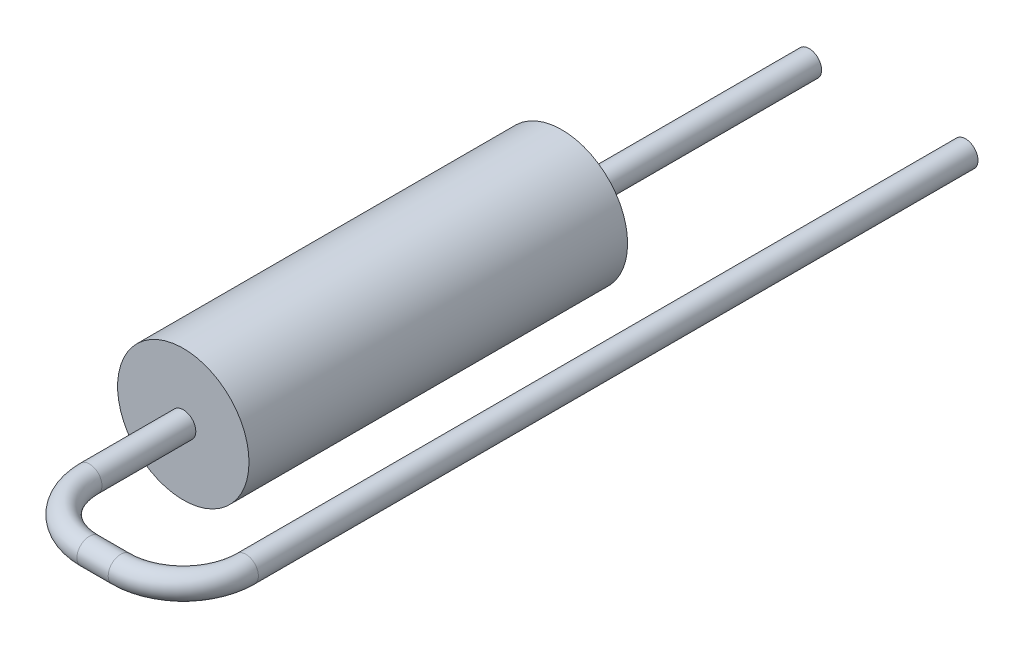
SolidWorks part; units mm, degrees
ref_plane "Front Plane" through (0, 0, 0) normal (0, 0, 1) x (1, 0, 0)
ref_plane "Top Plane" through (0, 0, 0) normal (0, 1, 0) x (1, 0, 0)
ref_plane "Right Plane" through (0, 0, 0) normal (1, 0, 0) x (0, 0, -1)
sketch "Sketch2" plane through (0, 0, 0) normal (0, 0, 1) x (1, 0, 0)
  circle A0 centre (0, 0) radius 2.1
  dimension "D1" = 4.2
extrude "Resistor Body" add sketch "Sketch2" along normal blind 12.1
sketch "Lead1 Path" plane through (0, 0, 0) normal (0, 1, 0) x (1, 0, 0)
  line L1 (-2.1, -12.1) -> (2.1, -12.1) construction
  line L2 (0, -12.1) -> (0, 0) construction
  line L3 (0, -12.1) -> (0, -15.1)
  line L4 (5, -15.1) -> (5, 7.9)
  line L5 (2, -17.1) -> (3, -17.1)
  arc A0 (2, -17.1) -> (0, -15.1) centre (2, -15.1) cw
  arc A1 (5, -15.1) -> (3, -17.1) centre (3, -15.1) cw
  point P11 (0, -17.1)
  point P14 (5, -17.1)
  dimension "D4" = 2
  dimension "D1" = 5
  dimension "D2" = 25
  dimension "D3" = 5
sketch "Lead1 Profile" plane through (0, 0, 12.1) normal (0, 0, 1) x (-1, 0, 0)
  circle A0 centre (0, 0) radius 0.4
  dimension "D1" = 0.8
sweep "Lead1" add profiles "Lead1 Profile" path "Lead1 Path"
sketch "Sketch6" plane through (0, 0, 0) normal (0, 0, -1) x (1, 0, 0)
  circle A0 centre (0, 0) radius 0.4 construction
  circle A1 centre (0, 0) radius 0.4
extrude "Lead2" add sketch "Sketch6" along normal up to surface (7.9 mm away) up to face at (4.6, 0, -7.9)
ref_plane "Mouting Plane" through (0, 0, -4) normal (0, 0, 1) x (1, 0, 0)
sketch "Component_Outline" plane through (0, 0, -4) normal (0, 0, 1) x (1, 0, 0)
  line L0 (2.0616, 0.4) -> (5, 0.4)
  line L1 (3, 0.4) -> (2, 0.4) construction
  line L2 (5, -0.4) -> (2.0616, -0.4)
  line L3 (2, -0.4) -> (3, -0.4) construction
  arc A0 (2.0616, 0.4) -> (2.0616, -0.4) centre (0, 0) ccw
  arc A1 (5, 0.4) -> (5, -0.4) centre (5, 0) cw
  circle A2 centre (5, 0) radius 0.4 construction
  dimension "D1" = 2.1
